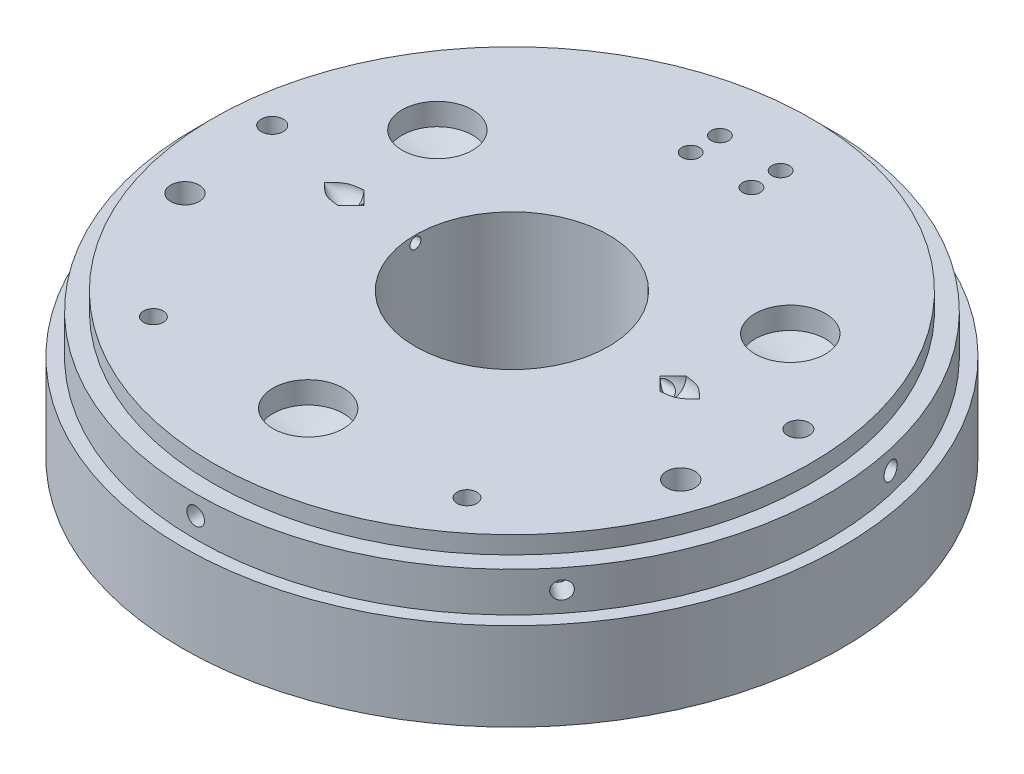
SolidWorks part; units mm, degrees
ref_plane "Front Plane" through (0, 0, 0) normal (0, 0, 1) x (1, 0, 0)
ref_plane "Top Plane" through (0, 0, 0) normal (0, 1, 0) x (1, 0, 0)
ref_plane "Right Plane" through (0, 0, 0) normal (1, 0, 0) x (0, 0, -1)
sketch "Sketch1" plane through (0, 0, 0) normal (0, 1, 0) x (1, 0, 0)
  circle A0 centre (0, 0) radius 150
extrude "Extrude1" add sketch "Sketch1" along normal blind 40
sketch "Sketch2" plane through (0, 40, 0) normal (0, 1, 0) x (1, 0, 0)
  circle A0 centre (0, 0) radius 144
extrude "Extrude2" add sketch "Sketch2" along normal blind 18
sketch "Sketch3" plane through (0, 58, 0) normal (0, 1, 0) x (1, 0, 0)
  circle A0 centre (0, 0) radius 136
extrude "Extrude4" add sketch "Sketch3" along normal blind 8
ref_plane "Plane3" through (0, 0, 144) normal (0, 0, 1) x (1, 0, 0)
sketch "Sketch5" plane through (0, 0, 144) normal (0, 0, 1) x (1, 0, 0)
  line L0 (0, 58) -> (0, 40) construction
  circle A0 centre (0, 49.2437) radius 4
sketch "Sketch7" plane through (0, 66, 0) normal (0, 1, 0) x (-1, 0, 0)
  circle A0 centre (0, 0) radius 44
extrude "Extrude11" cut sketch "Sketch7" against normal blind 100
sketch "Sketch11" plane through (0, 66, 0) normal (0, 1, 0) x (1, 0, 0)
  circle A0 centre (0, -92.7414) radius 16
extrude "Extrude12" cut sketch "Sketch11" against normal blind 10
pattern_circular "CirPattern4" count 3 over 360 about axis through (0, 0, 0) along (0, 1, 0) of "Extrude12"
sketch "Sketch14" plane through (0, 66, 0) normal (0, 1, 0) x (1, 0, 0)
  line L0 (0, 0) -> (-150, 0) construction
  line L1 (-73.357, 0) -> (-67.279, 0)
  line L2 (-73.357, 0) -> (-85.357, 0)
  line L4 (-73.357, 6) -> (-67.279, 0)
  circle A0 centre (0, 0) radius 150 construction
  spline S0 degree 3 poles (-85.357, 0) (-83.5017, 1.9201) (-80.1734, 5.3645) (-75.4482, 5.805) (-73.357, 6) knots 0 0 0 0 0.557436 1 1 1 1
revolve "Cut-Revolve1" cut sketch "Sketch14" angle 360 about L0
ref_plane "Plane5" through (-43, 0, 0) normal (1, 0, 0) x (0, 0, -1)
sketch "Sketch16" plane through (-43, 0, 0) normal (1, 0, 0) x (0, 0, -1)
  line L1 (0, 66.146) -> (0, 61.1606)
  circle A0 centre (0, 61.1606) radius 2.5
  circle A1 centre (0, 62.8196) radius 2.5
  point P5 (-41.2693, 49.3239)
pattern_circular "CirPattern5" count 2 over 360 about axis through (0, 40, 0) along (0, -1, 0) skipping 1 of "Cut-Revolve1"
extrude "Extrude13" cut sketch "Sketch16" against normal blind 30 contours A1
pattern_circular "CirPattern6" count 2 over 360 about axis through (0, 40, 0) along (0, -1, 0) of "Cut-Revolve1", "Extrude13"
sketch "Sketch18" plane through (0, 66, 0) normal (0, 1, 0) x (-1, 0, 0)
  circle A0 centre (-119.7225, -10.6228) radius 5
extrude "Extrude19" cut sketch "Sketch18" against normal blind 18
sketch "Sketch22" plane through (0, 66, 0) normal (0, 1, 0) x (-1, 0, 0)
  circle A0 centre (-112.8154, 35.9999) radius 6.5
extrude "Extrude20" cut sketch "Sketch22" against normal blind 18
sketch "Sketch23" plane through (0, 66, 0) normal (0, 1, 0) x (-1, 0, 0)
  circle A0 centre (-71.373, 91.832) radius 4.5
extrude "Extrude21" cut sketch "Sketch23" against normal blind 18
sketch "Sketch24" plane through (0, 66, 0) normal (0, 1, 0) x (-1, 0, 0)
  line L0 (0, 0) -> (0, -162.0027) construction
  circle A0 centre (-13.8141, -108.4729) radius 4
  circle A1 centre (-13.8141, -95.1851) radius 4
extrude "Extrude23" cut sketch "Sketch24" against normal blind 8
mirror "Mirror3" about plane through (0, 0, 0) normal (1, 0, 0) of "Extrude21", "Extrude20", "Extrude19", "Extrude23"
sketch "Sketch25" plane through (0, 56, 0) normal (0, 1, 0) x (1, 0, 0)
  circle A0 centre (-80.3164, 46.3707) radius 16
extrude "Extrude25" cut sketch "Sketch25" against normal blind 4 draft 75
pattern_circular "CirPattern7" count 3 over 360 about axis through (0, 0, 0) along (0, 1, 0) of "Extrude25"
sketch "Sketch27" plane through (0, 48, 0) normal (0, 1, 0) x (1, 0, 0)
  circle A0 centre (-119.7225, 10.6228) radius 5
extrude "Extrude27" cut sketch "Sketch27" against normal blind 2 draft 70
sketch "Sketch29" plane through (0, 48, 0) normal (0, 1, 0) x (1, 0, 0)
  circle A0 centre (-112.8154, -35.9999) radius 6.5
extrude "Extrude29" cut sketch "Sketch29" against normal blind 2 draft 75
sketch "Sketch30" plane through (0, 48, 0) normal (0, 1, 0) x (1, 0, 0)
  circle A0 centre (-71.373, -91.832) radius 4.5
extrude "Extrude30" cut sketch "Sketch30" against normal blind 2 draft 75
sketch "Sketch31" plane through (0, 58, 0) normal (0, 1, 0) x (1, 0, 0)
  circle A0 centre (-13.8141, 108.4729) radius 4
extrude "Extrude31" cut sketch "Sketch31" against normal blind 2 draft 75
sketch "Sketch32" plane through (0, 58, 0) normal (0, 1, 0) x (1, 0, 0)
  circle A0 centre (-13.8141, 95.1851) radius 4
extrude "Extrude32" cut sketch "Sketch32" against normal blind 2 draft 75
mirror "Mirror4" about plane through (0, 0, 0) normal (1, 0, 0) of "Extrude30", "Extrude29", "Extrude27", "Extrude32", "Extrude31"
extrude "Extrude33" cut sketch "Sketch5" against normal blind 10
sketch "Sketch33" plane through (0, 0, 134) normal (0, 0, 1) x (1, 0, 0)
  circle A0 centre (0, 49.2437) radius 2
extrude "Extrude34" cut sketch "Sketch33" against normal blind 5
sketch "Sketch34" plane through (0, 0, 129) normal (0, 0, 1) x (1, 0, 0)
  circle A0 centre (0, 49.2437) radius 2
extrude "Extrude36" cut sketch "Sketch34" against normal blind 1 draft 75
pattern_circular "CirPattern10" count 7 over 360 about axis through (0, 0, 0) along (0, 1, 0) of "Extrude36", "Extrude34", "Extrude33"
